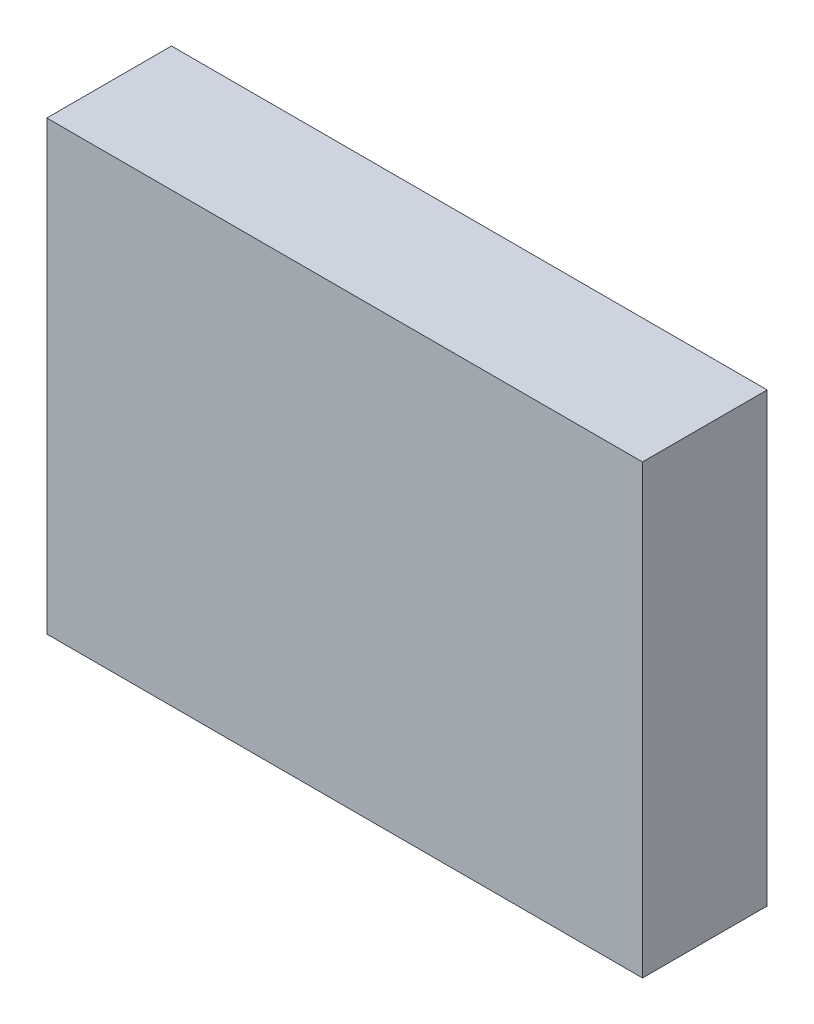
SolidWorks part; units mm, degrees
ref_plane "Front Plane" through (0, 0, 0) normal (0, 0, 1) x (1, 0, 0)
ref_plane "Top Plane" through (0, 0, 0) normal (0, 1, 0) x (1, 0, 0)
ref_plane "Right Plane" through (0, 0, 0) normal (1, 0, 0) x (0, 0, -1)
sketch "Sketch2" plane through (0, 0, 0) normal (0, 0, 1) x (1, 0, 0)
  line L0 (55.8333, 244) -> (279.1667, 244) construction
  line L1 (55.8333, 244) -> (279.1667, 244) construction
  line L2 (41.4514, 78.6271) -> (62.7178, 78.432)
  line L3 (62.7178, 78.432) -> (62.7178, 64.3845)
  line L4 (62.7178, 64.3845) -> (59.5961, 64.3845)
  line L5 (59.5961, 64.3845) -> (59.5961, 25.9489)
  line L6 (25.0626, 41.167) -> (38.7199, 40.9719)
  line L7 (59.5961, 25.9489) -> (50.4262, 15.9986)
  line L8 (50.4262, 15.9986) -> (32.8668, 16.1937)
  line L9 (38.7199, 40.9719) -> (38.7199, 30.2412)
  line L10 (38.7199, 30.2412) -> (44.1829, 30.2412)
  line L11 (44.1829, 30.2412) -> (45.7437, 32.5825)
  line L12 (45.7437, 32.5825) -> (45.5486, 64.3845)
  line L13 (45.5486, 64.3845) -> (41.2563, 64.3845)
  line L14 (41.2563, 64.3845) -> (41.4514, 78.6271)
  line L15 (133.6964, 60.4813) -> (333.6964, 60.4813) construction
  line L16 (105.0967, 161.1016) -> (305.0967, 161.1016) construction
  line L17 (73.0214, 78.8625) -> (105.898, 78.6116)
  line L18 (114.9328, 68.071) -> (114.6818, 49.7504)
  line L19 (114.6818, 49.7504) -> (105.898, 42.7234)
  line L20 (105.898, 42.7234) -> (90.338, 42.4724)
  line L21 (90.338, 42.4724) -> (90.5728, 27.9163)
  line L22 (90.5728, 27.9163) -> (93.6006, 27.9163)
  line L23 (73.0214, 18.6306) -> (93.6006, 18.6306)
  line L24 (78.0407, 27.9163) -> (78.0407, 69.8277)
  line L25 (78.0407, 27.9163) -> (73.0214, 27.9163)
  line L26 (93.6006, 18.6306) -> (93.6006, 27.9163)
  line L27 (78.0407, 69.8277) -> (73.0214, 69.8277)
  line L28 (73.0214, 18.6306) -> (73.0214, 27.9163)
  line L29 (73.0214, 69.8277) -> (73.0214, 78.8625)
  line L30 (105.898, 78.6116) -> (114.9328, 68.071)
  line L32 (88.5303, 69.8277) -> (88.5303, 53.1645)
  line L35 (99.0862, 69.8277) -> (103.2688, 64.9481)
  line L36 (88.5303, 69.8277) -> (99.0862, 69.8277)
  line L38 (88.5303, 53.1645) -> (99.0862, 53.1645)
  line L39 (99.0862, 53.1645) -> (103.2688, 56.7495)
  line L40 (103.2688, 56.7495) -> (103.2688, 64.9481)
  spline S0 degree 3 poles (32.8668, 16.1937) (31.9106, 17.628) (24.8725, 25.7517) (24.8675, 26.144) (24.8041, 31.1517) (24.9976, 36.1594) (25.0626, 41.167) knots 0 0 0 0 1 1 1 2 2 2 2
extrude "Boss-Extrude1" add sketch "Sketch2" along normal blind 18
ref_plane "Plane2" through (0, 0, 18) normal (0, 0, 1) x (1, 0, 0)
sketch "Sketch4" plane through (0, 0, 18) normal (0, 0, 1) x (1, 0, 0)
  line L5 (15.0626, 88.6271) -> (124.9328, 88.6271)
  line L6 (15.0626, 88.6271) -> (15.0626, 6.1937)
  line L7 (15.0626, 6.1937) -> (124.9328, 6.1937)
  line L8 (124.9328, 88.6271) -> (124.9328, 6.1937)
extrude "Boss-Extrude2" add sketch "Sketch4" along normal blind 5 and the other way blind 18 separate body
combine bodies "Combine1" operation type subtract main body 103 bodies to subtract 101 102
